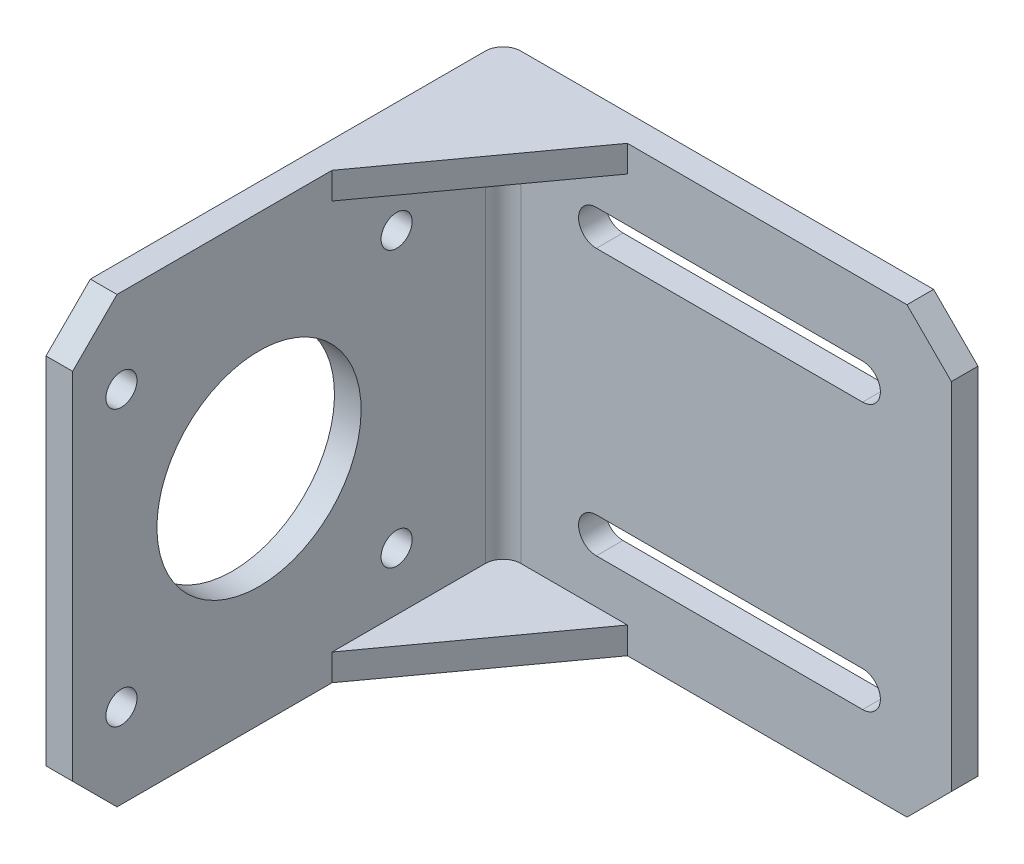
SolidWorks part; units mm, degrees
ref_plane "Front Plane" through (0, 0, 0) normal (0, 0, 1) x (1, 0, 0)
ref_plane "Top Plane" through (0, 0, 0) normal (0, 1, 0) x (1, 0, 0)
ref_plane "Right Plane" through (0, 0, 0) normal (1, 0, 0) x (0, 0, -1)
sketch "Sketch2" plane through (0, 0, 0) normal (0, 0, 1) x (1, 0, 0)
  line L1 (-26.75, 25) -> (26.75, 25)
  line L2 (-26.75, 25) -> (-26.75, -25)
  line L3 (-26.75, -25) -> (26.75, -25)
  line L4 (26.75, 25) -> (26.75, -25)
  line L5 (-26.75, 25) -> (26.75, -25) construction
  line L6 (-26.75, -25) -> (26.75, 25) construction
  point P0 (0, 0)
  dimension "D1" = 53.5
  dimension "D2" = 50
extrude "Boss-Extrude1" add sketch "Sketch2" along normal blind 51.5
sketch "Sketch3" plane through (0, 0, 51.5) normal (0, 0, 1) x (1, 0, 0)
  line L0 (-26.75, -25) -> (26.75, -25) construction
  line L1 (26.75, 25) -> (-23.75, 25)
  line L2 (26.75, 25) -> (26.75, -25)
  line L3 (26.75, -25) -> (-23.75, -25)
  line L4 (-23.75, 25) -> (-23.75, -25)
  dimension "D1" = 50.5
extrude "Cut-Extrude1" cut sketch "Sketch3" against normal blind 48.5
chamfer "Chamfer1" distance 14 angle 54 1 edges at (-23.75, 0, 3)
sketch "Sketch4" plane through (26.75, 0, 0) normal (1, 0, 0) x (0, 0, -1)
  line L0 (-3, -25) -> (-3, 25) construction
  line L1 (-3, 22) -> (-51.5, 22)
  line L2 (-3, 22) -> (-3, -22)
  line L3 (-3, -22) -> (-51.5, -22)
  line L4 (-51.5, 22) -> (-51.5, -22)
  line L5 (-51.5, 25) -> (-51.5, -25) construction
  dimension "D1" = 44
  dimension "D2" = 22
extrude "Cut-Extrude2" cut sketch "Sketch4" against normal blind 50.5
sketch "Sketch5" plane through (-26.75, 0, 0) normal (-1, 0, 0) x (0, 0, 1)
  line L0 (51.5, 25) -> (51.5, -25) construction
  line L1 (0, 25) -> (0, -25) construction
  circle A0 centre (46, 15.5) radius 1.75
  circle A1 centre (46, -15.5) radius 1.75
  circle A2 centre (15, 15.5) radius 1.75
  circle A3 centre (15, -15.5) radius 1.75
  circle A4 centre (30.5, 0) radius 11.5
  dimension "D1" = 3.5
  dimension "D2" = 3.5
  dimension "D3" = 3.5
  dimension "D4" = 3.5
  dimension "D15" = 23
  dimension "D5" = 31
  dimension "D6" = 31
  dimension "D7" = 31
  dimension "D8" = 31
  dimension "D9" = 15.5
  dimension "D10" = 15.5
  dimension "D11" = 5.5
  dimension "D12" = 5.5
  dimension "D13" = 15.5
  dimension "D14" = 15.5
extrude "Cut-Extrude3" cut sketch "Sketch5" against normal blind 10
sketch "Sketch6" plane through (0, 0, 3) normal (0, 0, 1) x (1, 0, 0)
  line L0 (-13.25, 15) -> (16.75, 15) construction
  line L1 (-13.25, 17) -> (16.75, 17)
  line L2 (-13.25, 13) -> (16.75, 13)
  line L3 (-13.25, -15) -> (16.75, -15) construction
  line L4 (-13.25, -13) -> (16.75, -13)
  line L5 (-13.25, -17) -> (16.75, -17)
  line L6 (26.75, -25) -> (26.75, 25) construction
  arc A0 (-13.25, 17) -> (-13.25, 13) centre (-13.25, 15) ccw
  arc A1 (16.75, 13) -> (16.75, 17) centre (16.75, 15) ccw
  arc A2 (-13.25, -13) -> (-13.25, -17) centre (-13.25, -15) ccw
  arc A3 (16.75, -17) -> (16.75, -13) centre (16.75, -15) ccw
  point P2 (1.75, 15)
  point P7 (1.75, -15)
  dimension "D1" = 4
  dimension "D2" = 4
  dimension "D3" = 26
  dimension "D4" = 13
  dimension "D5" = 10
  dimension "D6" = 10
  dimension "D7" = 30
  dimension "D8" = 30
extrude "Cut-Extrude4" cut sketch "Sketch6" against normal blind 10
chamfer "Chamfer2" distance 5 angle 45 4 edges at (26.75, -25, 1.5) (26.75, 25, 1.5) (-25.25, 25, 51.5) (-25.25, -25, 51.5)
fillet "Fillet1" radius 2 2 edges at (-26.75, 0, 0) (-23.75, 0, 3)
